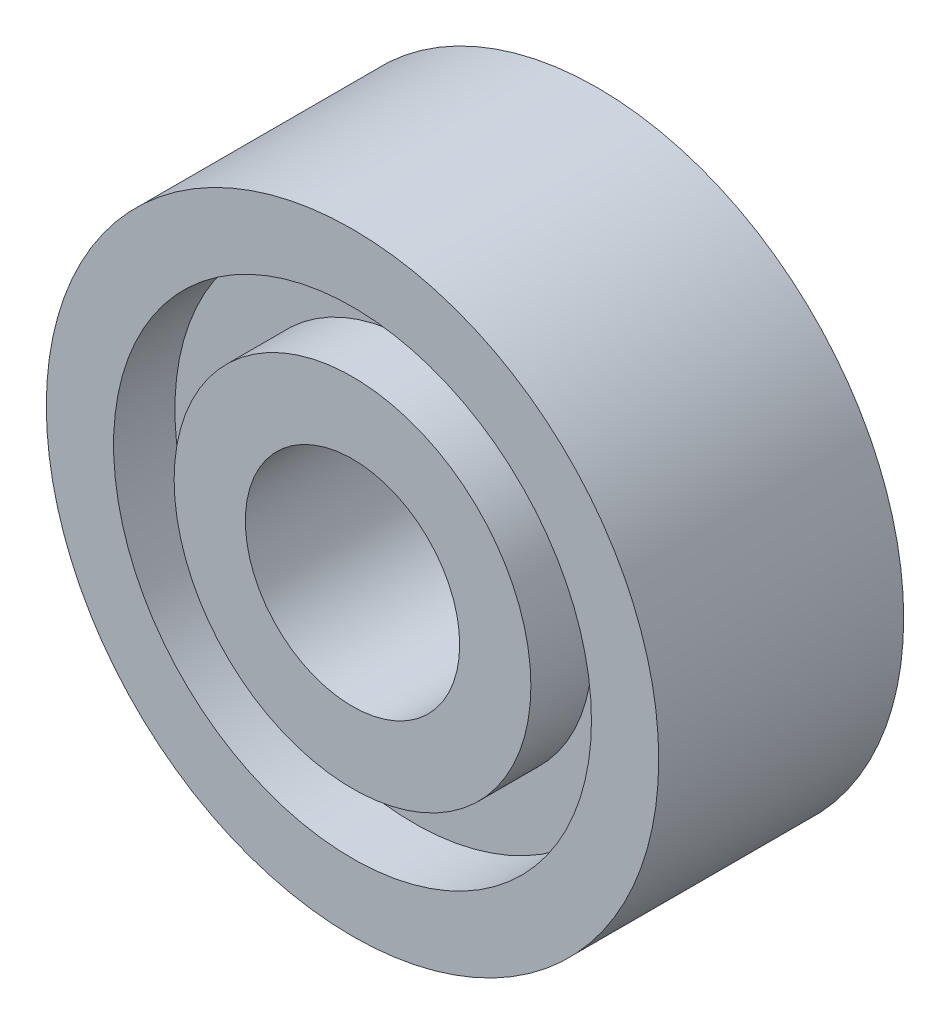
SolidWorks part; units mm, degrees
ref_plane "Спереди" through (0, 0, 0) normal (0, 0, 1) x (1, 0, 0)
ref_plane "Сверху" through (0, 0, 0) normal (0, 1, 0) x (1, 0, 0)
ref_plane "Справа" through (0, 0, 0) normal (1, 0, 0) x (0, 0, -1)
sketch "Эскиз2" plane through (0, 0, 0) normal (1, 0, 0) x (0, 0, -1)
  line L0 (-23.3143, 0) -> (33.6762, 0) construction
  line L1 (0, 10) -> (8, 10)
  line L2 (8, 10) -> (8, 7.8031)
  line L3 (8, 7.8031) -> (6.4324, 7.8031)
  line L4 (6.4324, 7.8031) -> (6.4324, 5.8254)
  line L5 (6.4324, 5.8254) -> (8, 5.8254)
  line L6 (8, 5.8254) -> (8, 3.5)
  line L7 (8, 3.5) -> (0, 3.5)
  line L8 (0, 3.5) -> (0, 5.8254)
  line L9 (0, 5.8254) -> (2.0022, 5.8254)
  line L10 (2.0022, 5.8254) -> (2.0022, 7.8031)
  line L11 (2.0022, 7.8031) -> (0, 7.8031)
  line L12 (0, 7.8031) -> (0, 10)
  point P5 (0, 0)
  point P16 (0, 0)
  point P17 (0, 0)
  point P18 (0, 0)
revolve "Повернуть1" add sketch "Эскиз2" angle 360 about L0
